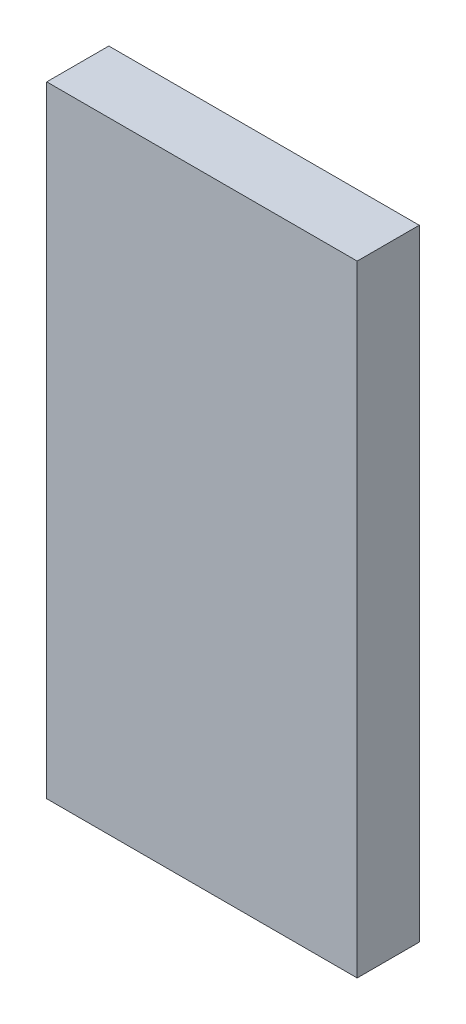
SolidWorks part; units mm, degrees
material "AISI 1020"
ref_plane "Alzado" through (0, 0, 0) normal (0, 0, 1) x (1, 0, 0)
ref_plane "Planta" through (0, 0, 0) normal (0, 1, 0) x (1, 0, 0)
ref_plane "Vista lateral" through (0, 0, 0) normal (1, 0, 0) x (0, 0, -1)
sketch "Croquis1" plane through (0, 0, 0) normal (0, 0, 1) x (1, 0, 0)
  line L1 (-30, -60) -> (30, -60)
  line L2 (-30, -60) -> (-30, 60)
  line L3 (-30, 60) -> (30, 60)
  line L4 (30, -60) -> (30, 60)
  line L5 (-30, -60) -> (30, 60) construction
  line L6 (-30, 60) -> (30, -60) construction
  point P0 (0, 0)
  dimension "D1" = 60
  dimension "D2" = 120
extrude "Saliente-Extruir1" add sketch "Croquis1" against normal blind 12
